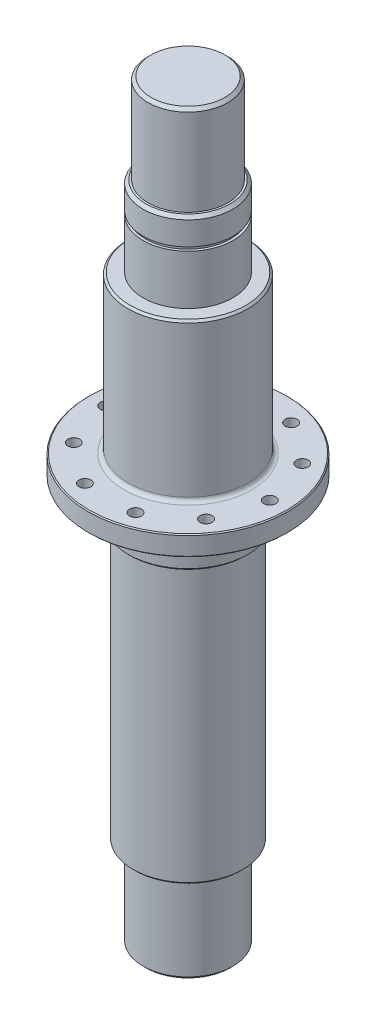
SolidWorks part; units mm, degrees
ref_plane "Ebene vorne" through (0, 0, 0) normal (0, 0, 1) x (1, 0, 0)
ref_plane "Ebene oben" through (0, 0, 0) normal (0, 1, 0) x (1, 0, 0)
ref_plane "Ebene rechts" through (0, 0, 0) normal (1, 0, 0) x (0, 0, -1)
sketch "Skizze1" plane through (0, 0, 0) normal (0, 1, 0) x (1, 0, 0)
  circle A0 centre (0, 0) radius 50
extrude "Aufsatz-Linear austragen1" add sketch "Skizze1" along normal blind 10
sketch "Skizze2" plane through (0, 10, 0) normal (0, 1, 0) x (1, 0, 0)
  line L0 (-50, 0) -> (50, 0) construction
  line L1 (0, 50) -> (0, -50) construction
  line L2 (0, 0) -> (-15.4508, 47.5528) construction
  line L3 (0, 0) -> (-40.4508, 29.3893) construction
  line L4 (0, 0) -> (-33.1697, -24.0992) construction
  line L5 (0, 0) -> (-12.6697, -38.9933) construction
  line L6 (0, 0) -> (12.6697, -38.9933) construction
  line L7 (0, 0) -> (33.1697, -24.0992) construction
  line L8 (0, 0) -> (12.6697, 38.9933) construction
  line L9 (0, 0) -> (33.1697, 24.0992) construction
  circle A0 centre (0, 0) radius 50 construction
  circle A1 centre (0, 0) radius 41
  circle A2 centre (-33.1697, 24.0992) radius 3
  circle A3 centre (33.1697, 24.0992) radius 3
  circle A4 centre (12.6697, 38.9933) radius 3
  circle A5 centre (41, 0) radius 3
  circle A6 centre (33.1697, -24.0992) radius 3
  circle A7 centre (12.6697, -38.9933) radius 3
  circle A8 centre (-12.6697, -38.9933) radius 3
  circle A9 centre (-33.1697, -24.0992) radius 3
  circle A10 centre (-41, 0) radius 3
  circle A11 centre (-12.6697, 38.9933) radius 3
  dimension "D1" = 82
  dimension "D2" = 36
  dimension "D3" = 18
  dimension "D4" = 36
  dimension "D5" = 36
  dimension "D6" = 36
  dimension "D7" = 36
  dimension "D8" = 18
  dimension "D9" = 36
extrude "Schnitt-Linear austragen2" cut sketch "Skizze2" against normal blind 10 contours A1 A2 | A1 A2 | A1 A11 | A1 A11 | A1 A4 | A1 A4 | A1 A10 | A1 A10 | A1 A9 | A1 A9 | A1 A8 | A1 A8 | A1 A7 | A1 A7 | A1 A6 | A1 A6 | A1 A5 | A1 A5 | A1 A3 | A1 A3
cosmetic thread "Gewindedarstellung1" parameters "D2"=8.5
cosmetic thread "Gewindedarstellung2" parameters "D2"=8.5
cosmetic thread "Gewindedarstellung3" parameters "D2"=8.5
cosmetic thread "Gewindedarstellung4" parameters "D2"=8.5
cosmetic thread "Gewindedarstellung5" parameters "D2"=8.5
cosmetic thread "Gewindedarstellung6" parameters "D2"=8.5
cosmetic thread "Gewindedarstellung7" parameters "D2"=8.5
cosmetic thread "Gewindedarstellung8" parameters "D2"=8.5
cosmetic thread "Gewindedarstellung9" parameters "D2"=8.5
cosmetic thread "Gewindedarstellung10" parameters "D2"=8.5
sketch "Skizze3" plane through (0, 10, 0) normal (0, 1, 0) x (1, 0, 0)
  circle A0 centre (0, 0) radius 30
extrude "Aufsatz-Linear austragen2" add sketch "Skizze3" along normal blind 78.6
fillet "Verrundung1" radius 2 1 edges at (0, 10, 30)
chamfer "Fase1" distance 1 angle 45 1 edges at (0, 88.6, 30)
sketch "Skizze4" plane through (0, 88.6, 0) normal (0, 1, 0) x (-1, 0, 0)
  circle A0 centre (0, 0) radius 22.5
extrude "Aufsatz-Linear austragen3" add sketch "Skizze4" along normal blind 24.9
sketch "Skizze5" plane through (0, 113.5, 0) normal (0, 1, 0) x (1, 0, 0)
  circle A0 centre (0, 0) radius 21.25
extrude "Aufsatz-Linear austragen4" add sketch "Skizze5" along normal blind 1.85
sketch "Skizze6" plane through (0, 115.35, 0) normal (0, 1, 0) x (1, 0, 0)
  circle A0 centre (0, 0) radius 22.5
extrude "Aufsatz-Linear austragen5" add sketch "Skizze6" along normal blind 13.25
chamfer "Fase2" distance 1.5 angle 45 1 edges at (0, 128.6, 22.5)
sketch "Skizze7" plane through (0, 128.6, 0) normal (0, 1, 0) x (1, 0, 0)
  circle A0 centre (0, 0) radius 20
extrude "Aufsatz-Linear austragen6" add sketch "Skizze7" along normal blind 45
chamfer "Fase3" distance 1.5 angle 45 1 edges at (0, 173.6, 20)
sketch "Skizze8" plane through (0, 0, 0) normal (0, -1, 0) x (1, 0, 0)
  circle A0 centre (0, 0) radius 30
extrude "Aufsatz-Linear austragen7" add sketch "Skizze8" along normal blind 20
chamfer "Fase4" distance 1 angle 45 1 edges at (0, -20, -30)
fillet "Verrundung2" radius 2 1 edges at (0, 0, 30)
chamfer "Fase5" distance 0.5 angle 45 1 edges at (0, 0, 50)
chamfer "Fase6" distance 0.5 angle 45 1 edges at (0, 10, 50)
sketch "Skizze9" plane through (0, -20, 0) normal (0, -1, 0) x (1, 0, 0)
  circle A0 centre (0, 0) radius 27.5
extrude "Aufsatz-Linear austragen8" add sketch "Skizze9" along normal blind 138
sketch "Skizze10" plane through (0, -158, 0) normal (0, -1, 0) x (1, 0, 0)
  circle A0 centre (0, 0) radius 22.5
extrude "Aufsatz-Linear austragen9" add sketch "Skizze10" along normal blind 45
fillet "Verrundung3" radius 1 1 edges at (0, -20, -27.5)
chamfer "Fase7" distance 1 angle 45 1 edges at (0, -158, -27.5)
fillet "Verrundung4" radius 1 1 edges at (0, -158, -22.5)
chamfer "Fase8" distance 1.5 angle 45 1 edges at (0, -203, -22.5)
sketch3d "3D-Skizze1"
  line L1 (-0.8821, 133.6, 20) -> (1.1179, 133.6, 20)
  line L2 (-5.8821, 138.6, 20) -> (-5.8821, 160.6, 20)
  line L3 (-0.8821, 165.6, 20) -> (1.1179, 165.6, 20)
  line L4 (6.1179, 138.6, 20) -> (6.1179, 160.6, 20)
  circle A0 centre (0, 173.6, 0) radius 18.5 construction
  arc A1 (-0.8821, 165.6, 20) -> (-5.8821, 160.6, 20) centre (-0.8821, 160.6, 20) ccw
  arc A2 (1.1179, 165.6, 20) -> (6.1179, 160.6, 20) centre (1.1179, 160.6, 20) ccw
  arc A3 (1.1179, 133.6, 20) -> (6.1179, 138.6, 20) centre (1.1179, 138.6, 20) ccw
  arc A4 (-0.8821, 133.6, 20) -> (-5.8821, 138.6, 20) centre (-0.8821, 138.6, 20) ccw
  point P6 (0, 192.1, 0)
  point P7 (0, 173.6, 20)
  point P8 (0, 173.6, 20)
  point P11 (-5.8821, 165.6, 20)
  point P12 (-0.8821, 160.6, 25)
  point P15 (6.1179, 165.6, 20)
  point P16 (1.1179, 160.6, 15)
  point P19 (6.1179, 133.6, 20)
  point P20 (1.1179, 138.6, 25)
  point P23 (-5.8821, 133.6, 20)
  point P24 (-0.8821, 138.6, 15)
  dimension "D2" = 8
  dimension "D4" = 5
  dimension "D1" = 32
  dimension "D3" = 12
